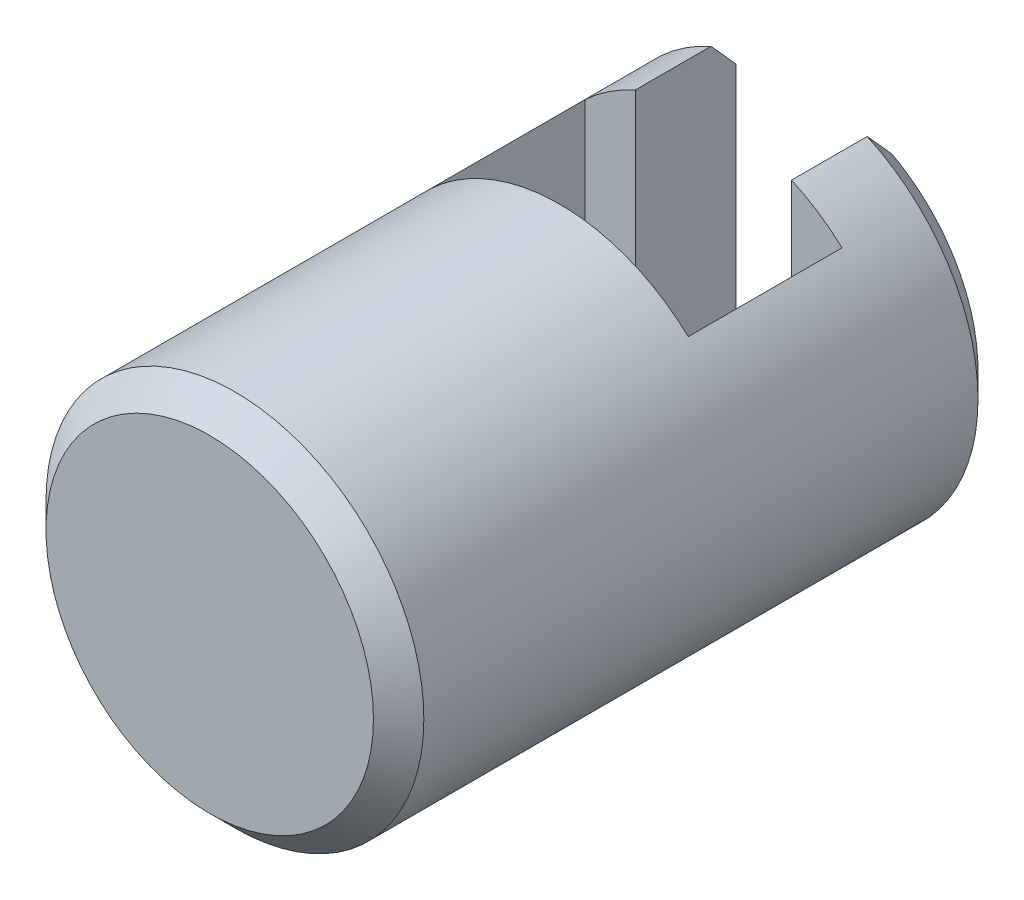
SolidWorks part; units mm, degrees
material "SKD61"
ref_plane "前视" through (0, 0, 0) normal (0, 0, 1) x (1, 0, 0)
ref_plane "上视" through (0, 0, 0) normal (0, 1, 0) x (1, 0, 0)
ref_plane "右视" through (0, 0, 0) normal (1, 0, 0) x (0, 0, -1)
sketch "草图1" plane through (0, 0, 0) normal (0, 0, 1) x (1, 0, 0)
  circle A0 centre (0, 0) radius 7.5
  dimension "D1" = 15
extrude "凸台-拉伸1" add sketch "草图1" along normal blind 24
sketch "草图2" plane through (0, 0, 0) normal (0, 1, 0) x (1, 0, 0)
  line L0 (0, 0) -> (0, -24) construction
  line L1 (-7.5, -24) -> (7.5, -24) construction
  line L2 (3.1, 0) -> (-3.1, 0)
  line L3 (7.5, 0) -> (-7.5, 0) construction
  line L4 (-3.1, 0) -> (-3.1, -4)
  line L5 (-3.1, -4) -> (-5.1, -4)
  line L6 (-5.1, -4) -> (-5.1, -10.1)
  line L7 (-5.1, -10.1) -> (5.1, -10.1)
  line L8 (5.1, -4) -> (5.1, -10.1)
  line L9 (3.1, -4) -> (5.1, -4)
  line L10 (3.1, 0) -> (3.1, -4)
  point P13 (0, -10.1)
  dimension "D1" = 10.2
  dimension "D2" = 6.2
  dimension "D3" = 6.1
  dimension "D4" = 4
extrude "切除-拉伸1" cut sketch "草图2" against normal mid plane 20
chamfer "倒角1" distance 1 angle 45 1 edges at (7.5, 0, 24)
chamfer "倒角2" distance 1 angle 45 2 edges at (7.5, 0, 0) (-7.5, 0, 0)
